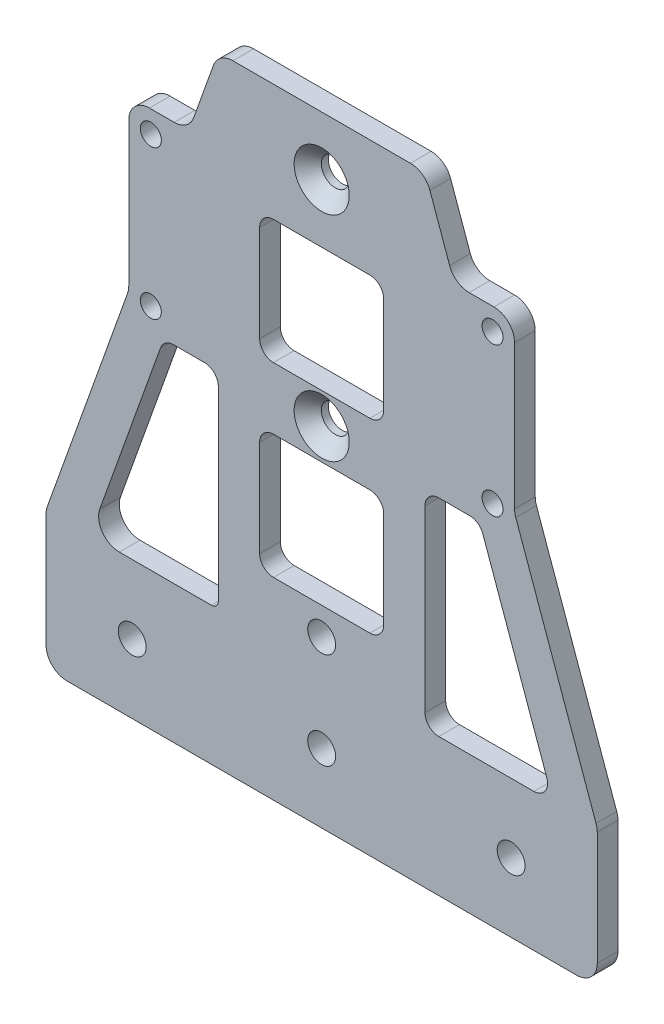
SolidWorks part; units mm, degrees
material "Thornel Mat VMA"
ref_plane "前视基准面" through (0, 0, 0) normal (0, 0, 1) x (1, 0, 0)
ref_plane "上视基准面" through (0, 0, 0) normal (0, 1, 0) x (1, 0, 0)
ref_plane "右视基准面" through (0, 0, 0) normal (1, 0, 0) x (0, 0, -1)
other "Configuration Table"
sketch "草图1" plane through (0, 0, 0) normal (0, 0, 1) x (1, 0, 0)
  line L8 (40, 0) -> (-40, 0)
  line L9 (-40, 0) -> (-40, 20)
  line L10 (-40, 20) -> (-15, 90)
  line L11 (-15, 90) -> (15, 90)
  line L12 (15, 90) -> (40, 20)
  line L13 (40, 20) -> (40, 0)
  line L14 (0, 0) -> (0, 90) construction
  dimension "D1" = 20
  dimension "D2" = 30
  dimension "D3" = 90
  dimension "D4" = 80
extrude "凸台-拉伸1" add sketch "草图1" along normal mid plane 3
sketch "草图2" plane through (0, 0, 1.5) normal (0, 0, 1) x (1, 0, 0)
  line L0 (-15, 72.1607) -> (-33.6288, 20)
  line L3 (-33.6288, 20) -> (-15, 20)
  line L10 (-15, 20) -> (-15, 72.1607)
  line L11 (-15, 90) -> (-40, 20) construction
  line L12 (-40, 0) -> (40, 0) construction
  line L13 (-40, 20) -> (-40, 0) construction
  line L14 (0, 0) -> (0, 28) construction
  line L15 (-9, 55) -> (9, 55)
  line L16 (-9, 55) -> (-9, 73)
  line L17 (-9, 73) -> (9, 73)
  line L18 (9, 55) -> (9, 73)
  line L19 (-9, 55) -> (9, 73) construction
  line L20 (-9, 73) -> (9, 55) construction
  line L21 (-9, 28) -> (9, 28)
  line L22 (-9, 28) -> (-9, 46)
  line L23 (-9, 46) -> (9, 46)
  line L24 (9, 28) -> (9, 46)
  line L25 (-9, 28) -> (9, 46) construction
  line L26 (-9, 46) -> (9, 28) construction
  line L27 (15, 20) -> (15, 72.1607)
  line L28 (33.6288, 20) -> (15, 20)
  line L29 (15, 72.1607) -> (33.6288, 20)
  point P2 (0, 37)
  point P11 (0, 64)
  dimension "D1" = 6
  dimension "D5" = 28
  dimension "D2" = 20
  dimension "D3" = 25
  dimension "D4" = 18
  dimension "D6" = 9
extrude "切除-拉伸1" cut sketch "草图2" against normal up to surface (3 mm away) up to face at (0, 36.6667, -1.5)
fillet "圆角1" radius 1 2 edges at (-15, 20, 0) (-15, 72.1607, 0)
fillet "圆角2" radius 2 8 edges at (9, 73, 0) (9, 55, 0) (-9, 55, 0) (-9, 73, 0) (9, 28, 0) (-9, 46, 0) (9, 46, 0) (-9, 28, 0)
fillet "圆角3" radius 3 6 edges at (40, 0, 0) (-40, 0, 0) (-40, 20, 0) (15, 90, 0) (40, 20, 0) (-15, 90, 0)
sketch "草图3" plane through (0, 0, 1.5) normal (0, 0, 1) x (1, 0, 0)
  line L0 (-37, 0) -> (37, 0) construction
  line L1 (0, 0) -> (0, 28) construction
  line L2 (-7, 28) -> (7, 28) construction
  circle A0 centre (-27.5, 10) radius 2.025
  circle A1 centre (27.5, 10) radius 2.025
  dimension "D1" = 55
  dimension "D2" = 4.05
  dimension "D3" = 10
extrude "切除-拉伸2" cut sketch "草图3" against normal through all both and the other way through all
sketch "草图4" plane through (0, 0, 1.5) normal (0, 0, 1) x (1, 0, 0)
  line L0 (-27.5, 10) -> (0, 10) construction
  circle A0 centre (0, 10) radius 2.025
  dimension "D1" = 4.05
extrude "切除-拉伸3" cut sketch "草图4" against normal through all both
sketch "草图5" plane through (0, 0, 1.5) normal (0, 0, 1) x (1, 0, 0)
  line L0 (-7, 28) -> (7, 28) construction
  line L1 (0, 55) -> (0, 46) construction
  line L2 (-7, 55) -> (7, 55) construction
  line L3 (7, 46) -> (-7, 46) construction
  line L4 (0, 73) -> (0, 90) construction
  line L5 (7, 73) -> (-7, 73) construction
  line L6 (12.8858, 90) -> (-12.8858, 90) construction
  circle A0 centre (0, 24) radius 2.025
  circle A1 centre (0, 50.5) radius 2.025
  circle A2 centre (0, 81.5) radius 2.025
  dimension "D1" = 4.05
  dimension "D2" = 4
extrude "切除-拉伸4" cut sketch "草图5" against normal through all both
fillet "圆角4" radius 3 1 edges at (-33.6288, 20, 0)
sketch "草图6" plane through (0, 0, -1.5) normal (0, 0, -1) x (-1, 0, 0)
  line L0 (28, 50) -> (-28, 50) construction
  line L1 (-28, 50) -> (28, 50)
  line L2 (-28, 50) -> (-28, 78)
  line L3 (-28, 78) -> (28, 78)
  line L4 (28, 50) -> (28, 78)
  line L5 (-28, 50) -> (28, 78) construction
  line L6 (-28, 78) -> (28, 50) construction
  line L7 (-39.8252, 20.4894) -> (-15.7111, 88.009) construction
  line L8 (15.7111, 88.009) -> (39.8252, 20.4894) construction
  line L9 (-39.8252, 20.4894) -> (-15.7111, 88.009)
  line L10 (15.7111, 88.009) -> (39.8252, 20.4894)
  line L11 (15, 21) -> (15, 66.3875) construction
  line L12 (16.9417, 66.7238) -> (32.197, 24.009) construction
  line L15 (15, 21) -> (15, 66.3875)
  line L16 (16.9417, 66.7238) -> (32.197, 24.009)
  arc A0 (16.9417, 66.7238) -> (15, 66.3875) centre (16, 66.3875) ccw construction
  arc A2 (16.9417, 66.7238) -> (15, 66.3875) centre (16, 66.3875) ccw
  point P0 (0, 64)
extrude "凸台-拉伸2" add sketch "草图6" against normal up to surface (3 mm away)
fillet "圆角5" radius 3 6 edges at (-28, 53.6, 0) (-19.2857, 78, 0) (19.2857, 78, 0) (28, 78, 0) (28, 53.6, 0) (-28, 78, 0)
sketch "草图7" plane through (0, 0, -1.5) normal (0, 0, -1) x (-1, 0, 0)
  line L0 (-12.8858, 90) -> (12.8858, 90) construction
  line L1 (-24.8, 53.2) -> (24.8, 53.2) construction
  line L2 (-24.8, 53.2) -> (-24.8, 74.8) construction
  line L3 (-24.8, 74.8) -> (24.8, 74.8) construction
  line L4 (24.8, 53.2) -> (24.8, 74.8) construction
  line L5 (-24.8, 53.2) -> (24.8, 74.8) construction
  line L6 (-24.8, 74.8) -> (24.8, 53.2) construction
  line L9 (18.9573, 50) -> (18.9573, 78) construction
  line L10 (15, 50) -> (22.9145, 50) construction
  line L11 (21.3999, 78) -> (25, 78) construction
  circle A0 centre (24.8, 74.8) radius 1.525
  circle A1 centre (24.8, 53.2) radius 1.525
  circle A2 centre (-24.8, 53.2) radius 1.525
  circle A3 centre (-24.8, 74.8) radius 1.525
  point P0 (0, 64)
  point P7 (0, 90)
  point P8 (0, 74.8)
  point P16 (18.9573, 64)
  dimension "D3" = 3.05
  dimension "D1" = 21.6
  dimension "D2" = 49.6
extrude "切除-拉伸5" cut sketch "草图7" against normal up to surface (3 mm away) up to face at (-21.886, 30.6782, 1.5)
hole_wizard "孔1" positions "草图8" profile "草图9" legacy
sketch "草图8" plane through (0, 0, 1.5) normal (0, 0, 1) x (1, 0, 0)
  point P0 (0, 81.5)
  point P3 (0, 50.5)
sketch "草图9" plane through (0, 81.5, 1.5) normal (1, 0, 0) x (0, -1, 0)
  line L0 (0, 0) -> (0, 100)
  line L1 (0, 100) -> (2.025, 100)
  line L2 (2.025, 100) -> (2.025, 1.975)
  line L3 (2.025, 1.975) -> (4, 0)
  line L4 (4, 0) -> (0, 0)
  line L5 (0, -6.4453) -> (0, 115.525) construction
  line L6 (-2.025, 1.975) -> (-4, 0) construction
  dimension "直径" = 4.05
  dimension "深度" = 100
  dimension "锥坑角度" = 90
  dimension "锥坑直径" = 8
fillet "圆角6" radius 2 6 edges at (15, 20, 0) (33.6288, 20, 0) (22.9145, 50, 0) (15, 50, 0) (-22.9145, 50, 0) (-15, 50, 0)
